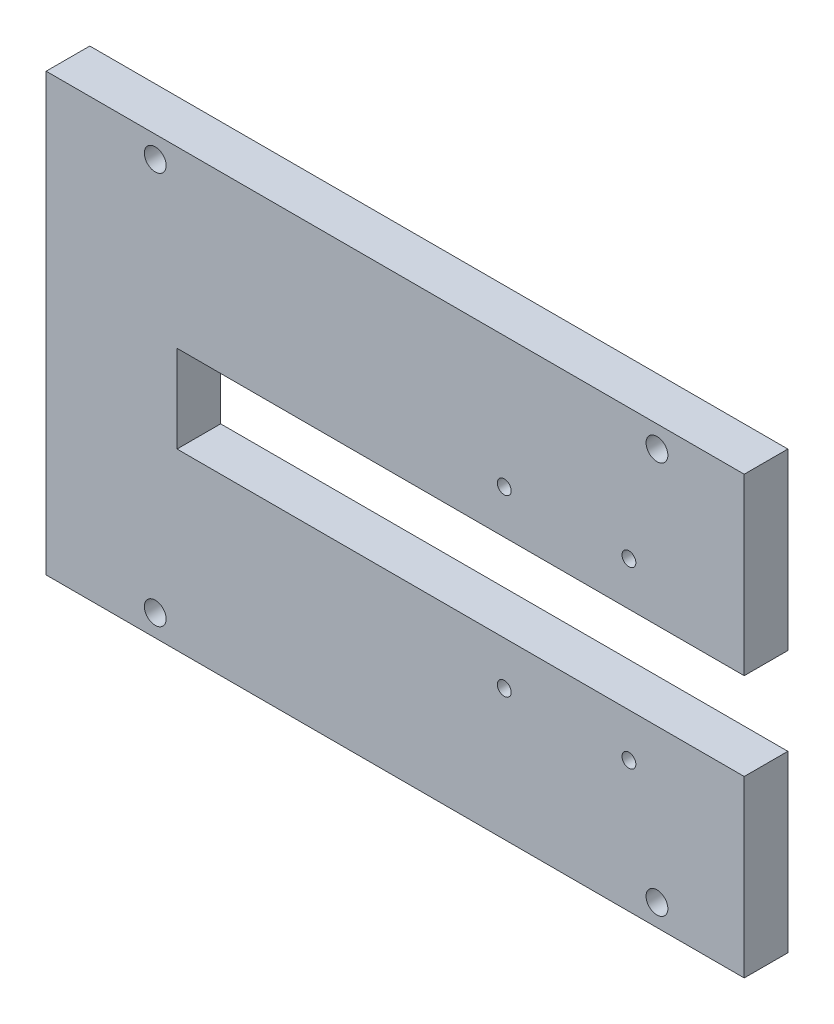
SolidWorks part; units mm, degrees
ref_plane "Front Plane" through (0, 0, 0) normal (0, 0, 1) x (1, 0, 0)
ref_plane "Top Plane" through (0, 0, 0) normal (0, 1, 0) x (1, 0, 0)
ref_plane "Right Plane" through (0, 0, 0) normal (1, 0, 0) x (0, 0, -1)
sketch "Sketch1" plane through (0, 0, 0) normal (0, 0, 1) x (1, 0, 0)
  line L0 (-53.5376, 64.885) -> (106.4624, 64.885)
  line L1 (-53.5376, -35.115) -> (106.4624, -35.115)
  line L2 (-53.5376, 64.885) -> (-53.5376, -35.115)
  line L3 (106.4624, 64.885) -> (106.4624, 24.885)
  line L4 (106.4624, -35.115) -> (106.4624, 4.885)
  line L5 (106.4624, 4.885) -> (-23.5376, 4.885)
  line L6 (106.4624, 24.885) -> (-23.5376, 24.885)
  line L7 (-23.5376, 24.885) -> (-23.5376, 4.885)
  circle A0 centre (51.4624, 34.885) radius 1.5875
  circle A1 centre (80.0374, 34.885) radius 1.5875
  circle A2 centre (51.4624, -5.115) radius 1.5875
  circle A3 centre (80.0374, -5.115) radius 1.5875
  circle A4 centre (-28.5376, 59.885) radius 2.5
  circle A5 centre (86.4624, 59.885) radius 2.5
  circle A6 centre (-28.5376, -30.115) radius 2.5
  circle A7 centre (86.4624, -30.115) radius 2.5
  dimension "D3" = 55
  dimension "D4" = 3.175
  dimension "D7" = 10
  dimension "D10" = 5
  dimension "D13" = 5
  dimension "D16" = 5
  dimension "D19" = 5
  dimension "D1" = 100
  dimension "D2" = 160
  dimension "D5" = 28.575
  dimension "D6" = 10
  dimension "D8" = 40
  dimension "D9" = 130
  dimension "D11" = 5
  dimension "D12" = 25
  dimension "D14" = 5
  dimension "D15" = 20
  dimension "D17" = 25
  dimension "D18" = 5
  dimension "D20" = 5
  dimension "D21" = 20
extrude "Boss-Extrude1" add sketch "Sketch1" along normal blind 10
